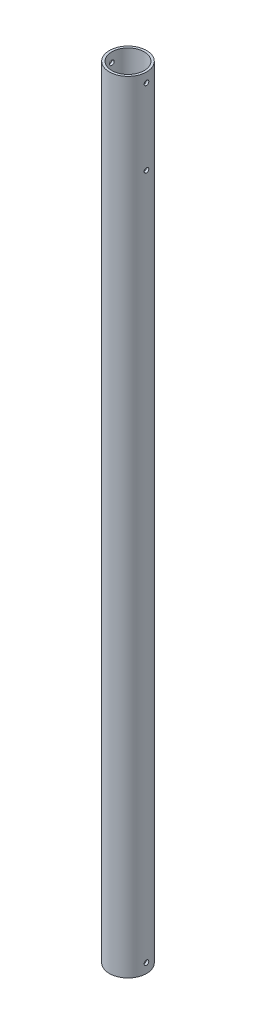
SolidWorks part; units mm, degrees
ref_plane "Front" through (0, 0, 0) normal (0, 0, 1) x (1, 0, 0)
ref_plane "Top" through (0, 0, 0) normal (0, 1, 0) x (1, 0, 0)
ref_plane "Right" through (0, 0, 0) normal (1, 0, 0) x (0, 0, -1)
sketch "Sketch1" plane through (0, 0, 0) normal (0, 1, 0) x (1, 0, 0)
  circle A0 centre (0, 0) radius 21.797
  circle A1 centre (0, 0) radius 24.972
  dimension "D1" = 49.944
  dimension "D2" = 3.175
extrude "Boss-Extrude1" add sketch "Sketch1" along normal blind 1047.75
sketch "Sketch2" plane through (0, 0, 0) normal (1, 0, 0) x (0, 0, -1)
  line L0 (0, 0) -> (0, 12.7) construction
  circle A0 centre (0, 12.7) radius 3.1115
  dimension "D1" = 12.7
  dimension "D2" = 6.223
extrude "Cut-Extrude1" cut sketch "Sketch2" against normal through all both and the other way through all
ref_plane "Plane1" through (0, 523.875, 0) normal (0, 1, 0) x (1, 0, 0)
mirror "Mirror1" about plane through (0, 523.875, 0) normal (0, 1, 0) of "Cut-Extrude1"
sketch "Sketch3" plane through (0, 0, 0) normal (1, 0, 0) x (0, 0, -1)
  line L0 (0, 1047.75) -> (0, 933.45) construction
  line L1 (24.972, 1047.75) -> (-24.972, 1047.75) construction
  circle A0 centre (0, 933.45) radius 3.1115
  circle A1 centre (0, 1035.05) radius 3.1115 construction
  dimension "D1" = 114.3
extrude "Cut-Extrude3" cut sketch "Sketch3" against normal through all both and the other way through all
